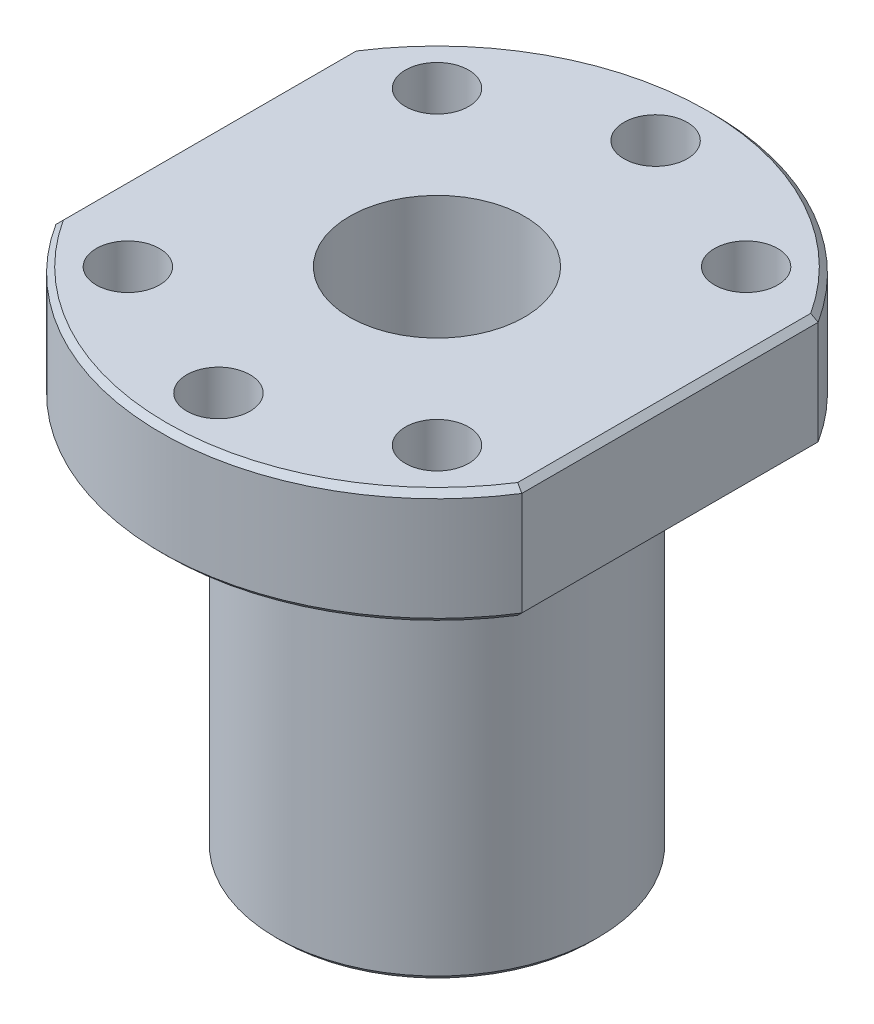
SolidWorks part; units mm, degrees
ref_plane "Спереди" through (0, 0, 0) normal (0, 0, 1) x (1, 0, 0)
ref_plane "Сверху" through (0, 0, 0) normal (0, 1, 0) x (1, 0, 0)
ref_plane "Справа" through (0, 0, 0) normal (1, 0, 0) x (0, 0, -1)
sketch "Эскиз1" plane through (0, 0, 0) normal (0, 1, 0) x (1, 0, 0)
  circle A0 centre (0, 0) radius 14
  dimension "D1" = 28
extrude "Бобышка-Вытянуть1" add sketch "Эскиз1" along normal blind 34
sketch "Эскиз2" plane through (0, 34, 0) normal (0, 1, 0) x (1, 0, 0)
  line L2 (-20.25, -12.8817) -> (-20.25, 12.8817)
  line L4 (20.25, -12.8817) -> (20.25, 12.8817)
  line L5 (-15.1061, -18.6495) -> (15.1061, 18.6495) construction
  line L6 (-15.1061, 18.6495) -> (15.1061, -18.6495) construction
  arc A0 (20.25, 12.8817) -> (-20.25, 12.8817) centre (0, 0) ccw
  arc A1 (-20.25, -12.8817) -> (20.25, -12.8817) centre (0, 0) ccw
  circle A2 centre (0, 0) radius 19 construction
  circle A3 centre (0, 19) radius 2.75
  circle A4 centre (13.435, 13.435) radius 2.75
  circle A6 centre (13.435, -13.435) radius 2.75
  circle A7 centre (0, -19) radius 2.75
  circle A8 centre (-13.435, -13.435) radius 2.75
  circle A10 centre (-13.435, 13.435) radius 2.75
  circle A11 centre (-19, 0) radius 2.75 [skipped]
  circle A12 centre (19, 0) radius 2.75 [skipped]
  point P30 (0, 0)
  dimension "D1" = 48
  dimension "D2" = 38
  dimension "D3" = 5.5
  dimension "D4" = 8
extrude "Бобышка-Вытянуть2" add sketch "Эскиз2" along normal blind 10
sketch "Эскиз3" plane through (0, 44, 0) normal (0, 1, 0) x (1, 0, 0)
  circle A0 centre (0, 0) radius 7.6
  dimension "D1" = 15.2
extrude "Вырез-Вытянуть1" cut sketch "Эскиз3" against normal through all
chamfer "Фаска1" distance 0.5 angle 45 9 edges at (0, 34, 24) (20.25, 34, 0) (0, 34, -24) (-20.25, 34, 0) (0, 44, -24) (20.25, 44, 0) (0, 44, 24) (-20.25, 44, 0) (0, 0, 14)
